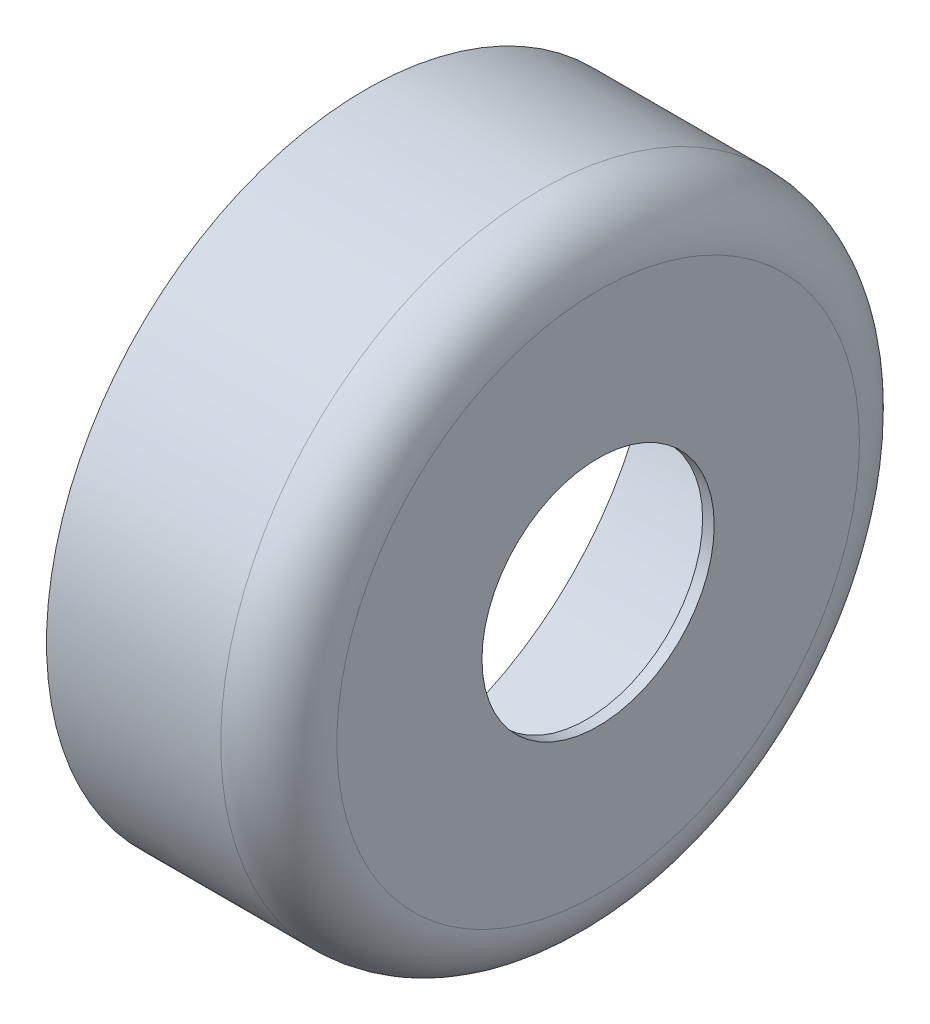
SolidWorks part; units mm, degrees
ref_plane "Front Plane" through (0, 0, 0) normal (0, 0, 1) x (1, 0, 0)
ref_plane "Top Plane" through (0, 0, 0) normal (0, 1, 0) x (1, 0, 0)
ref_plane "Right Plane" through (0, 0, 0) normal (1, 0, 0) x (0, 0, -1)
sketch "Sketch1" plane through (0, 0, 0) normal (1, 0, 0) x (0, 0, -1)
  circle A0 centre (0, 0) radius 55
  dimension "110" = 110
extrude "Boss-Extrude1" add sketch "Sketch1" along normal blind 40
sketch "Sketch2" plane through (0, 0, 0) normal (-1, 0, 0) x (0, 0, 1)
  circle A0 centre (0, 0) radius 50
  dimension "D1" = 100
extrude "Cut-Extrude1" cut sketch "Sketch2" against normal blind 38
sketch "Sketch3" plane through (40, 0, 0) normal (1, 0, 0) x (0, 0, -1)
  circle A0 centre (0, 0) radius 20
  dimension "D1" = 40
extrude "Cut-Extrude2" cut sketch "Sketch3" against normal blind 38
fillet "Fillet1" radius 10 1 edges at (40, 0, -55)
